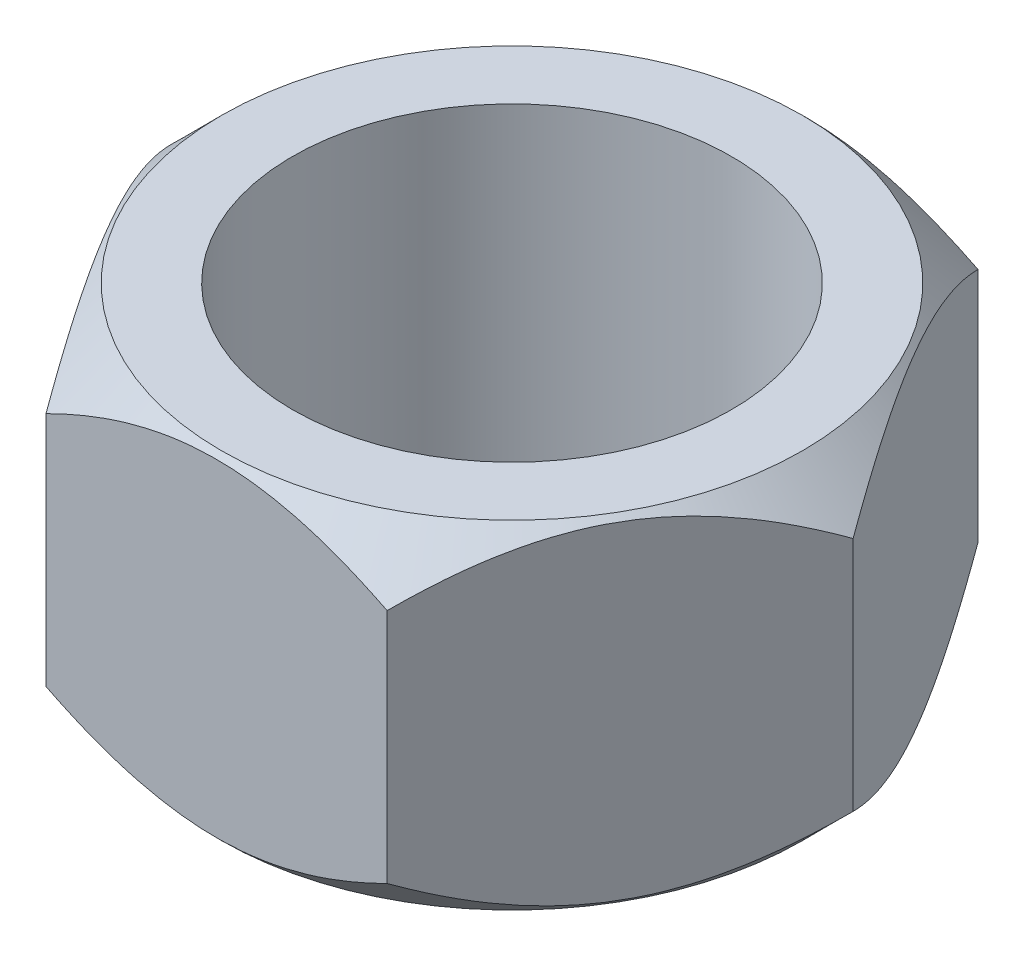
SolidWorks part; units mm, degrees
ref_plane "Front Plane" through (0, 0, 0) normal (0, 0, 1) x (1, 0, 0)
ref_plane "Top Plane" through (0, 0, 0) normal (0, 1, 0) x (1, 0, 0)
ref_plane "Right Plane" through (0, 0, 0) normal (1, 0, 0) x (0, 0, -1)
sketch "Sketch2" plane through (0, 0, 0) normal (0, 1, 0) x (1, 0, 0)
  line L1 (0.2021, 0) -> (0.101, 0.175)
  line L2 (0.101, 0.175) -> (-0.101, 0.175)
  line L3 (-0.101, 0.175) -> (-0.2021, 0)
  line L4 (-0.2021, 0) -> (-0.101, -0.175)
  line L5 (-0.101, -0.175) -> (0.101, -0.175)
  line L6 (0.101, -0.175) -> (0.2021, 0)
  circle A0 centre (0, 0) radius 0.175 construction
  dimension "D1" = 0.35
extrude "Boss-Extrude1" add sketch "Sketch2" along normal blind 0.2
sketch "Sketch4" plane through (0, 0.2, 0) normal (0, 1, 0) x (1, 0, 0)
  circle A0 centre (0, 0) radius 0.13
  dimension "D1" = 0.26
extrude "Cut-Extrude2" cut sketch "Sketch4" against normal up to next
sketch "Sketch5" plane through (0, 0, 0) normal (0, 0, 1) x (1, 0, 0)
  line L0 (0.101, 0) -> (0.2021, 0) construction
  line L2 (0.101, 0.2) -> (0.2021, 0.2) construction
  line L3 (0.2021, 0) -> (0.1721, 0)
  line L4 (0.2021, 0.17) -> (0.2021, 0.2)
  line L5 (0.2021, 0.2) -> (0.1721, 0.2)
  line L6 (0.1721, 0.2) -> (0.2021, 0.17)
  line L7 (0.1721, 0) -> (0.2021, 0.03)
  line L8 (0.2021, 0.03) -> (0.2021, 0)
  line L9 (0, 0) -> (0, 0.0685) construction
revolve "Cut-Revolve1" cut sketch "Sketch5" angle 360 about L9
